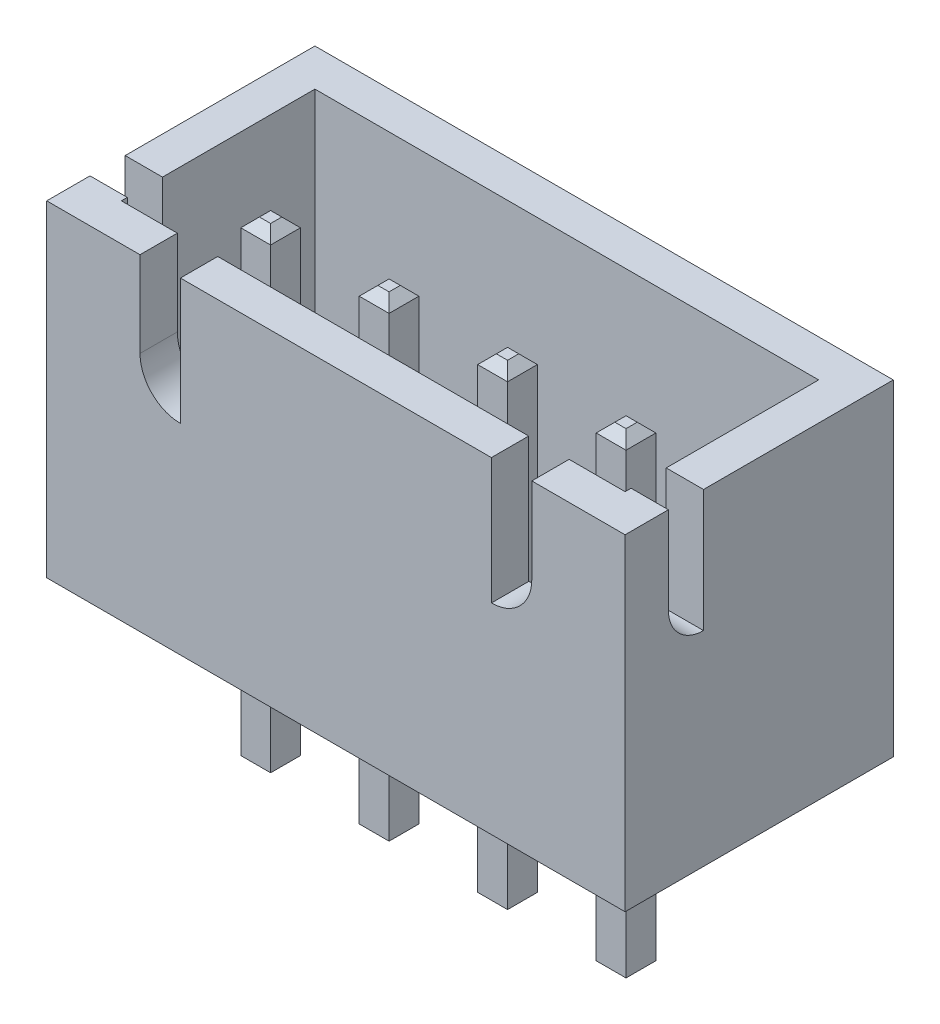
SolidWorks part; units mm, degrees
other "Camera1"
ref_plane "Front Plane" through (0, 0, 0) normal (0, 0, 1) x (1, 0, 0)
ref_plane "Top Plane" through (0, 0, 0) normal (0, 1, 0) x (1, 0, 0)
ref_plane "Right Plane" through (0, 0, 0) normal (1, 0, 0) x (0, 0, -1)
sketch "Sketch1" plane through (0, 0, 0) normal (0, 1, 0) x (1, 0, 0)
  line L1 (-6.2, 2.875) -> (6.2, 2.875)
  line L2 (-6.2, 2.875) -> (-6.2, -2.875)
  line L3 (-6.2, -2.875) -> (6.2, -2.875)
  line L4 (6.2, 2.875) -> (6.2, -2.875)
  line L5 (-6.2, 2.875) -> (6.2, -2.875) construction
  line L6 (-6.2, -2.875) -> (6.2, 2.875) construction
  point P0 (0, 0)
  dimension "D1" = 5.75
  dimension "D2" = 12.4
extrude "Boss-Extrude1" add sketch "Sketch1" along normal blind 7
shell "Shell1" thickness 0.8
sketch "Sketch2" plane through (6.2, 0, 0) normal (1, 0, 0) x (0, 0, -1)
  line L0 (-1.193, 7) -> (-1.193, 4.3796)
  line L1 (-2.875, 7) -> (2.875, 7) construction
  line L2 (-1.9469, 5.1335) -> (-1.9469, 7)
  line L3 (-1.9469, 7) -> (-1.193, 7)
  arc A0 (-1.193, 4.3796) -> (-1.9469, 5.1335) centre (-1.193, 5.1335) cw
extrude "Cut-Extrude1" cut sketch "Sketch2" against normal through all
sketch "Sketch3" plane through (0, 0, 2.875) normal (0, 0, 1) x (1, 0, 0)
  line L0 (-4.2, 7) -> (-4.2, 6.7289)
  line L1 (-6.2, 7) -> (6.2, 7) construction
  line L4 (-4.2, 6.7289) -> (-4.2, 5.1663)
  line L5 (-3.3338, 4.3001) -> (-3.3338, 7)
  line L6 (-3.3338, 7) -> (-4.2, 7)
  line L7 (-6.2, 7) -> (-6.2, 0) construction
  line L8 (0, 7) -> (0, 0) construction
  line L9 (3.3338, 7) -> (4.2, 7)
  line L10 (3.3338, 4.3001) -> (3.3338, 7)
  line L11 (4.2, 6.7289) -> (4.2, 5.1663)
  line L14 (4.2, 7) -> (4.2, 6.7289)
  arc A0 (-4.2, 5.1663) -> (-3.3338, 4.3001) centre (-3.3338, 5.1663) ccw
  arc A1 (4.2, 5.1663) -> (3.3338, 4.3001) centre (3.3338, 5.1663) cw
  dimension "D1" = 2
extrude "Cut-Extrude2" cut sketch "Sketch3" against normal up to next
sketch "Sketch4" plane through (0, 0, 0) normal (0, -1, 0) x (1, 0, 0)
  line L0 (-6.2, -2.875) -> (-6.2, 2.875) construction
  line L1 (-4.07, 0.845) -> (-3.43, 0.845)
  line L2 (-4.07, 0.845) -> (-4.07, 0.205)
  line L3 (-4.07, 0.205) -> (-3.43, 0.205)
  line L4 (-3.43, 0.845) -> (-3.43, 0.205)
  line L5 (-4.07, 0.845) -> (-3.43, 0.205) construction
  line L6 (-4.07, 0.205) -> (-3.43, 0.845) construction
  line L9 (-6.2, 2.875) -> (6.2, 2.875) construction
  line L10 (-1.53, 0.845) -> (-0.89, 0.845)
  line L11 (-0.89, 0.845) -> (-0.89, 0.205)
  line L12 (-1.53, 0.205) -> (-0.89, 0.205)
  line L13 (-1.53, 0.845) -> (-1.53, 0.205)
  line L14 (1.01, 0.845) -> (1.65, 0.845)
  line L15 (1.65, 0.845) -> (1.65, 0.205)
  line L16 (1.01, 0.205) -> (1.65, 0.205)
  line L17 (1.01, 0.845) -> (1.01, 0.205)
  line L18 (3.55, 0.845) -> (4.19, 0.845)
  line L19 (4.19, 0.845) -> (4.19, 0.205)
  line L20 (3.55, 0.205) -> (4.19, 0.205)
  line L21 (3.55, 0.845) -> (3.55, 0.205)
  point P0 (-3.75, 0.525)
  dimension "D1" = 0.64
  dimension "D2" = 0.64
  dimension "D3" = 2.45
  dimension "D4" = 2.35
  dimension "D5" = 4
extrude "Boss-Extrude2" add sketch "Sketch4" along normal blind 3.45 and the other way blind 6.75
chamfer "Chamfer1" distance 0.2 angle 45 32 edges at (3.55, -3.45, 0.525) (3.87, -3.45, 0.845) (4.19, -3.45, 0.525) (3.87, -3.45, 0.205) (1.01, -3.45, 0.525) (1.33, -3.45, 0.845) (1.65, -3.45, 0.525) (1.33, -3.45, 0.205) (-1.53, -3.45, 0.525) (-1.21, -3.45, 0.845) (-0.89, -3.45, 0.525) (-1.21, -3.45, 0.205) (-3.75, -3.45, 0.205) (-4.07, -3.45, 0.525) (-3.75, -3.45, 0.845) (-3.43, -3.45, 0.525) (4.19, 6.75, 0.525) (3.87, 6.75, 0.845) (3.55, 6.75, 0.525) (3.87, 6.75, 0.205) (1.65, 6.75, 0.525) (1.33, 6.75, 0.845) (1.01, 6.75, 0.525) (1.33, 6.75, 0.205) (-0.89, 6.75, 0.525) (-1.21, 6.75, 0.845) (-1.53, 6.75, 0.525) (-1.21, 6.75, 0.205) (-3.75, 6.75, 0.845) (-4.07, 6.75, 0.525) (-3.75, 6.75, 0.205) (-3.43, 6.75, 0.525)
